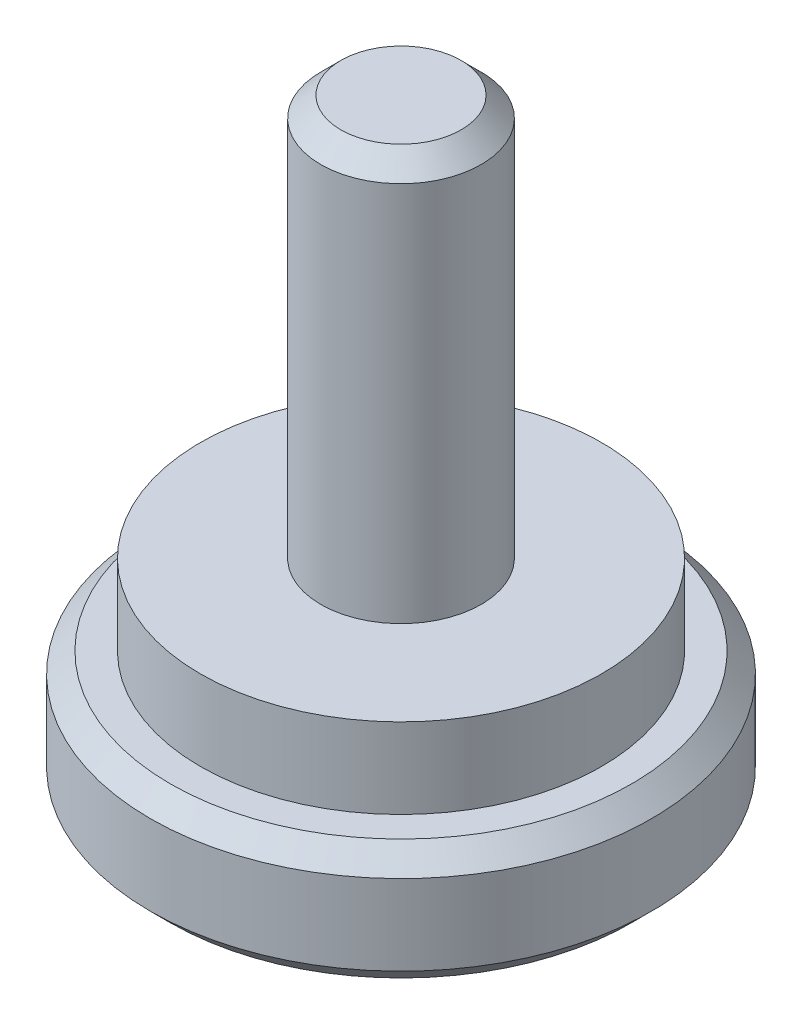
SolidWorks part; units mm, degrees
ref_plane "Face" through (0, 0, 0) normal (0, 0, 1) x (1, 0, 0)
ref_plane "Dessus" through (0, 0, 0) normal (0, 1, 0) x (1, 0, 0)
ref_plane "Droite" through (0, 0, 0) normal (1, 0, 0) x (0, 0, -1)
sketch "Esquisse1" plane through (0, 0, 0) normal (0, 1, 0) x (1, 0, 0)
  circle A0 centre (0, 0) radius 6.25
  dimension "D1" = 12.5
extrude "Extrusion1" add sketch "Esquisse1" along normal blind 3
sketch "Esquisse2" plane through (0, 3, 0) normal (0, 1, 0) x (1, 0, 0)
  circle A0 centre (0, 0) radius 5
  dimension "D1" = 10
extrude "Extrusion2" add sketch "Esquisse2" along normal blind 2
sketch "Esquisse3" plane through (0, 5, 0) normal (0, 1, 0) x (1, 0, 0)
  circle A0 centre (0, 0) radius 2
  dimension "D1" = 4
extrude "Extrusion3" add sketch "Esquisse3" along normal blind 10
chamfer "Chanfrein1" distance 0.5 angle 45 2 edges at (0, 3, 6.25) (0, 0, 6.25)
chamfer "Chanfrein2" distance 0.5 angle 45 1 edges at (0, 15, 2)
sketch "Esquisse4" plane through (0, 0, 0) normal (0, -1, 0) x (1, 0, 0)
  line L1 (0, 2.3094) -> (-2, 1.1547)
  line L2 (-2, 1.1547) -> (-2, -1.1547)
  line L3 (-2, -1.1547) -> (0, -2.3094)
  line L4 (0, -2.3094) -> (2, -1.1547)
  line L5 (2, -1.1547) -> (2, 1.1547)
  line L6 (2, 1.1547) -> (0, 2.3094)
  circle A0 centre (0, 0) radius 2 construction
  dimension "D1" = 4
extrude "Extrusion4" cut sketch "Esquisse4" against normal blind 4
